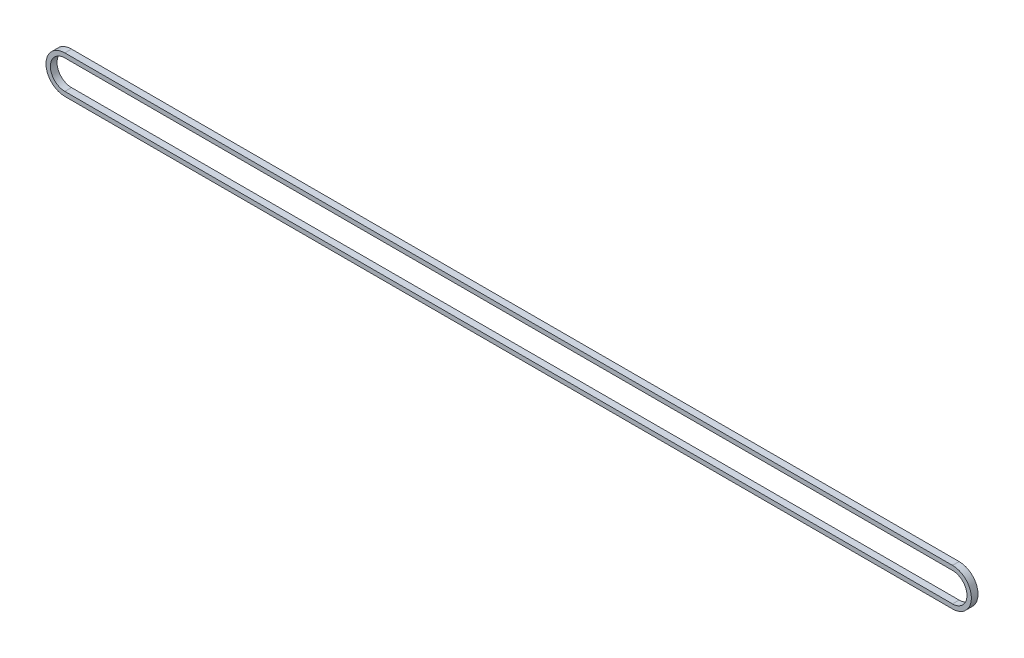
SolidWorks part; units mm, degrees
ref_plane "Front Plane" through (0, 0, 0) normal (0, 0, 1) x (1, 0, 0)
ref_plane "Top Plane" through (0, 0, 0) normal (0, 1, 0) x (1, 0, 0)
ref_plane "Right Plane" through (0, 0, 0) normal (1, 0, 0) x (0, 0, -1)
sketch "Sketch1" plane through (0, 0, 0) normal (0, 0, 1) x (1, 0, 0)
  line L0 (0, 22.3097) -> (1187.45, 22.3097)
  line L1 (0, -22.3097) -> (1187.45, -22.3097)
  line L2 (0, 0) -> (1187.45, 0) construction
  arc A0 (0, 22.3097) -> (0, -22.3097) centre (0, 0) ccw
  arc A1 (1187.45, -22.3097) -> (1187.45, 22.3097) centre (1187.45, 0) ccw
  dimension "D2" = 44.6194
  dimension "D3" = 44.6194
  dimension "D1" = 1187.45
extrude "Extrude-Thin1" add sketch "Sketch1" along normal mid plane 8.89 thin thin type mid plane wall 5.842
equation "\"Center Distance\"= 46.75"
equation "\"D1@Sketch1\"=\"Center Distance\""
equation "\"Pitch\"= 0.25"
equation "\"T1\"= 22"
equation "\"T2\"= 22"
equation "\"D2@Sketch1\"=\"Pitch\"/(sin( 180/\"T1\"))"
equation "\"D3@Sketch1\"=\"Pitch\"/(sin( 180/\"T2\"))"
equation "\"Links\"= 2 * \"Center Distance\" / \"Pitch\" + ( \"T1\" + \"T2\" ) / 2 + ( ( \"T2\" - \"T1\" ) / ( 2 * 3.14159 ) ) ^ 2 * \"Pitch\" / \"Center Distance\""
